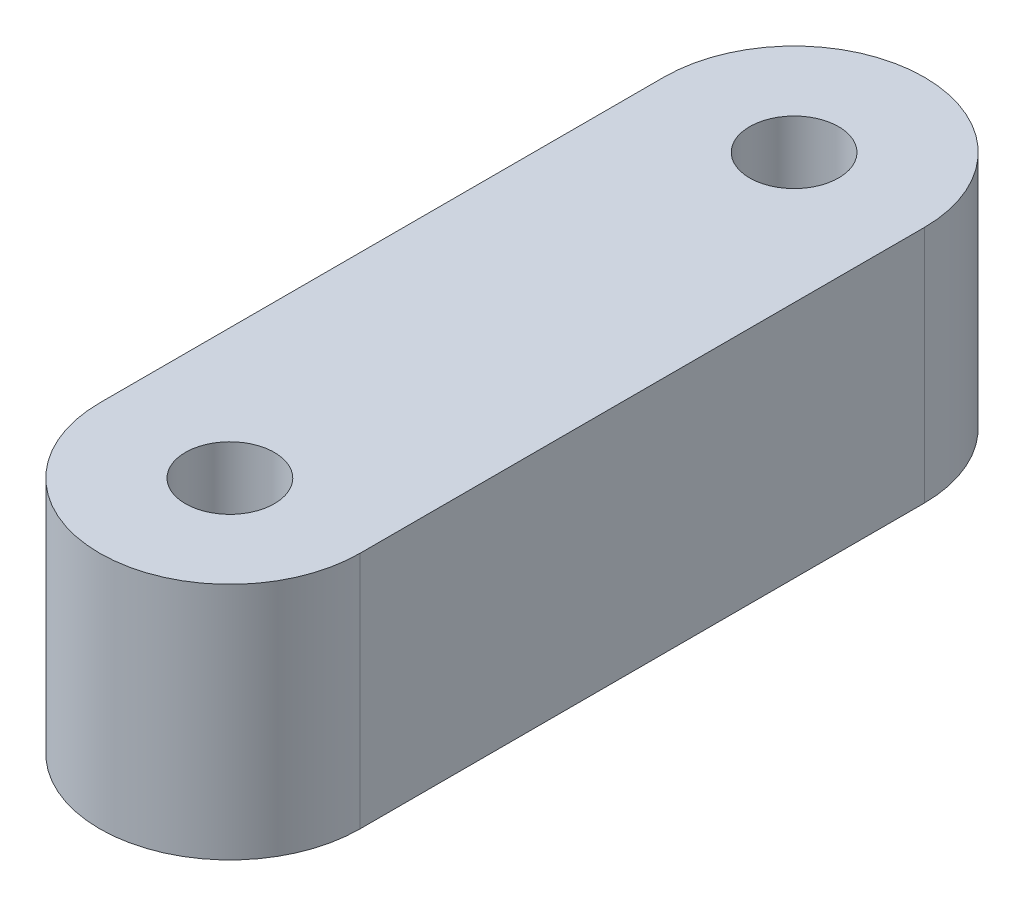
SolidWorks part; units mm, degrees
ref_plane "前视基准面" through (0, 0, 0) normal (0, 0, 1) x (1, 0, 0)
ref_plane "上视基准面" through (0, 0, 0) normal (0, 1, 0) x (1, 0, 0)
ref_plane "右视基准面" through (0, 0, 0) normal (1, 0, 0) x (0, 0, -1)
sketch "草图1" plane through (0, 0, 0) normal (0, 1, 0) x (1, 0, 0)
  line L0 (0, -13) -> (0, 13) construction
  line L1 (-6, -13) -> (-6, 13)
  line L2 (6, -13) -> (6, 13)
  arc A0 (-6, -13) -> (6, -13) centre (0, -13) ccw
  arc A1 (6, 13) -> (-6, 13) centre (0, 13) ccw
  point P2 (0, 0)
  dimension "D1" = 26
  dimension "D2" = 12
extrude "凸台-拉伸1" add sketch "草图1" along normal blind 11
sketch "草图2" plane through (0, 11, 0) normal (0, 1, 0) x (1, 0, 0)
  circle A0 centre (0, 13) radius 2.05
  circle A1 centre (0, -13) radius 2.05
  dimension "D1" = 13
  dimension "D3" = 4.1
  dimension "D4" = 4.1
  dimension "D5" = 0
  dimension "D6" = 0
  dimension "D2" = 13
extrude "切除-拉伸1" cut sketch "草图2" against normal through all
sketch "草图3" plane through (-6, 0, 0) normal (-1, 0, 0) x (0, 0, 1)
  line L0 (-13, 0) -> (13, 0) construction
  circle A0 centre (0, 5.5) radius 3.6
  dimension "D1" = 5.5
  dimension "D2" = 7.2
extrude "切除-拉伸2" cut sketch "草图3" against normal blind 10
sketch "草图4" plane through (-6, 0, 0) normal (-1, 0, 0) x (0, 0, 1)
  line L1 (-5, -3.45) -> (5, -3.45)
  line L2 (-5, -3.45) -> (-5, 3.45)
  line L3 (-5, 3.45) -> (5, 3.45)
  line L4 (5, -3.45) -> (5, 3.45)
  line L5 (-5, -3.45) -> (5, 3.45) construction
  line L6 (-5, 3.45) -> (5, -3.45) construction
  circle A0 centre (0, 5.5) radius 3.6
  point P3 (0, 0)
  circle M5 centre (0, 5.5) radius 3.6
  dimension "D1" = 10
  dimension "D2" = 2.05
extrude "凸台-拉伸3" add sketch "草图4" against normal blind 10 contours L3 M5
